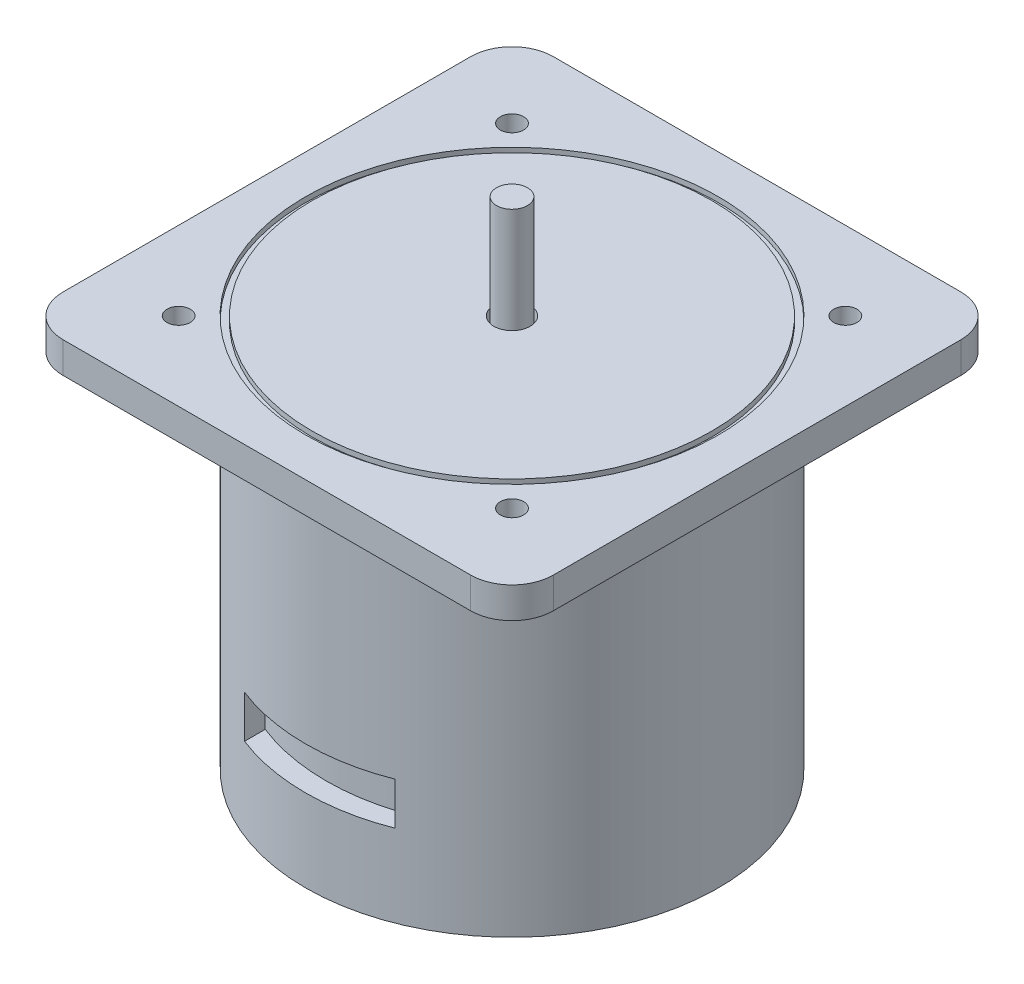
SolidWorks part; units mm, degrees
ref_plane "Front Plane" through (0, 0, 0) normal (0, 0, 1) x (1, 0, 0)
ref_plane "Top Plane" through (0, 0, 0) normal (0, 1, 0) x (1, 0, 0)
ref_plane "Right Plane" through (0, 0, 0) normal (1, 0, 0) x (0, 0, -1)
sketch "Sketch1" plane through (0, 0, 0) normal (0, 1, 0) x (1, 0, 0)
  circle A0 centre (0, 0) radius 40
  dimension "D1" = 80
extrude "Boss-Extrude1" add sketch "Sketch1" along normal blind 70
sketch "Sketch2" plane through (0, 70, 0) normal (0, 1, 0) x (1, 0, 0)
  line L1 (-47.5, 47.5) -> (47.5, 47.5)
  line L2 (-47.5, 47.5) -> (-47.5, -47.5)
  line L3 (-47.5, -47.5) -> (47.5, -47.5)
  line L4 (47.5, 47.5) -> (47.5, -47.5)
  line L5 (-47.5, 47.5) -> (47.5, -47.5) construction
  line L6 (-47.5, -47.5) -> (47.5, 47.5) construction
  point P0 (0, 0)
  dimension "D1" = 95
  dimension "D2" = 95
extrude "Boss-Extrude2" add sketch "Sketch2" along normal blind 6
sketch "Sketch3" plane through (0, 76, 0) normal (0, 1, 0) x (1, 0, 0)
  circle A0 centre (0, 0) radius 40
  circle A1 centre (0, 0) radius 38.7093
  dimension "D1" = 80
extrude "Cut-Extrude1" cut sketch "Sketch3" against normal blind 1
sketch "Sketch4" plane through (0, 76, 0) normal (0, 1, 0) x (1, 0, 0)
  circle A0 centre (0, 0) radius 3
  dimension "D1" = 6
extrude "Boss-Extrude3" add sketch "Sketch4" along normal blind 20 contours A0
sketch "Sketch5" plane through (0, 76, 0) normal (0, 1, 0) x (1, 0, 0)
  line L0 (41.1066, -41.1066) -> (47.5, -47.5) construction
  point P15 (0, 0)
fillet "Fillet1" radius 8 4 edges at (47.5, 73, 47.5) (-47.5, 73, 47.5) (-47.5, 73, -47.5) (47.5, 73, -47.5)
sketch "Sketch6" plane through (0, 76, 0) normal (0, 1, 0) x (1, 0, 0)
  circle A0 centre (0, 0) radius 3
  circle A1 centre (0, 0) radius 3.5196
extrude "Cut-Extrude3" cut sketch "Sketch6" against normal blind 5
sketch "Sketch8" plane through (0, 0, 0) normal (0, 0, 1) x (1, 0, 0)
  line L1 (-14.5736, 24.1663) -> (14.5736, 24.1663)
  line L2 (-14.5736, 24.1663) -> (-14.5736, 15.9453)
  line L3 (-14.5736, 15.9453) -> (14.5736, 15.9453)
  line L4 (14.5736, 24.1663) -> (14.5736, 15.9453)
  line L5 (-14.5736, 24.1663) -> (14.5736, 15.9453) construction
  line L6 (-14.5736, 15.9453) -> (14.5736, 24.1663) construction
  point P0 (0, 20.0558)
extrude "Cut-Extrude4" cut sketch "Sketch8" against normal blind 4 from surface starting at face at (0, 70, 40)
sketch "Sketch9" plane through (0, 0, 0) normal (0, -1, 0) x (1, 0, 0)
  line L0 (-25.7729, 4.2733) -> (-27.3191, 6.2899)
  line L1 (-25.6227, -4.3844) -> (-27.098, -6.4534)
  arc A0 (-25.6227, -4.3844) -> (-25.7729, 4.2733) centre (-22.4965, 0) cw
  arc A1 (-30.4224, 0) -> (-27.098, -6.4534) centre (-22.4965, 0) ccw
  arc A2 (-27.3191, 6.2899) -> (-27.098, -6.4534) centre (-22.4965, 0) ccw
extrude "Boss-Extrude5" add sketch "Sketch9" along normal blind 4 contours L0 A2 A1 L1 A0
mirror "Mirror1" about plane through (0, 0, 0) normal (1, 0, 0) of "Boss-Extrude5"
sketch "Sketch10" plane through (0, 76, 0) normal (0, 1, 0) x (1, 0, 0)
  line L0 (41.1066, -41.1066) -> (47.5, -47.5) construction
  circle A1 centre (-32.2956, 32.2956) radius 2.25
  circle A2 centre (32.2956, 32.2956) radius 2.25
  circle A3 centre (32.2956, -32.2956) radius 2.25
  circle A4 centre (-32.2956, -32.2956) radius 2.25
  point P16 (0, 0)
  dimension "D2" = 4.5
  dimension "D3" = 4
extrude "Cut-Extrude5" cut sketch "Sketch10" against normal blind 34
